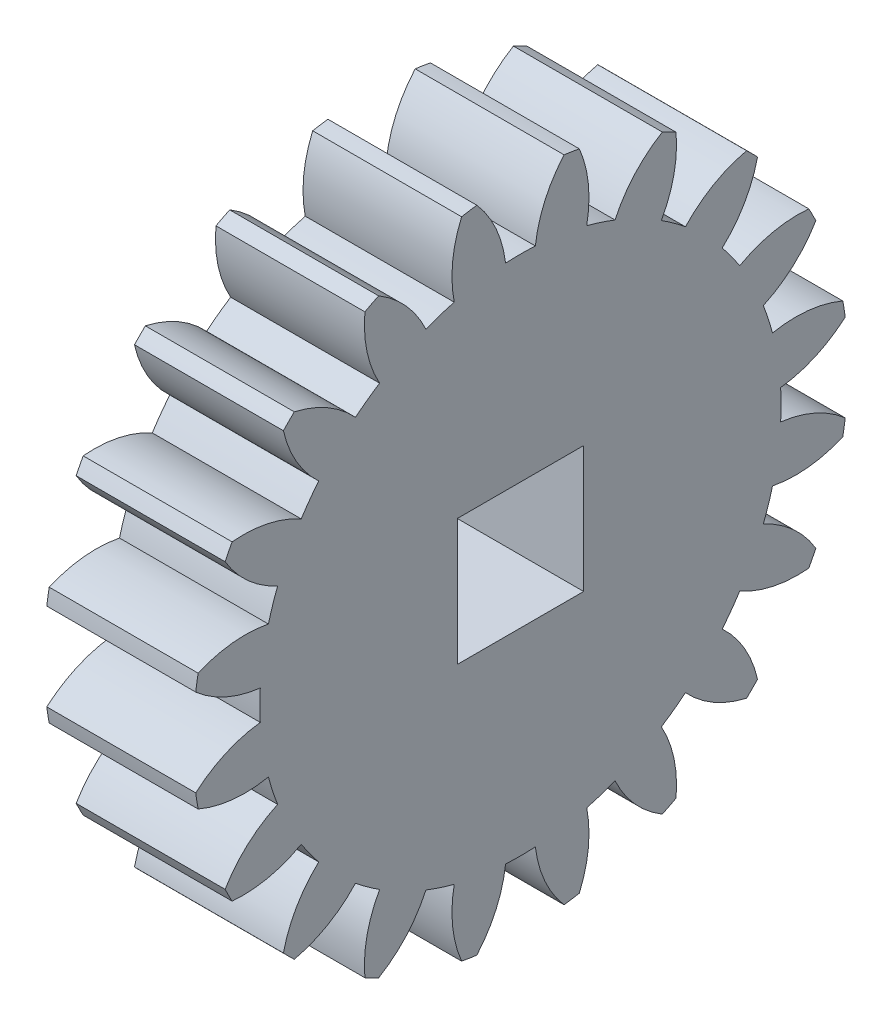
SolidWorks part; units mm, degrees
ref_plane "Plane1" through (0, 0, 0) normal (0, 0, 1) x (1, 0, 0)
ref_plane "Plane2" through (0, 0, 0) normal (0, 1, 0) x (1, 0, 0)
ref_plane "Plane3" through (0, 0, 0) normal (1, 0, 0) x (0, 0, -1)
other "Configuration Table"
sketch "HoldingSke" plane through (0, 0, 0) normal (0, 1, 0) x (1, 0, 0)
  line L0 (0, 0) -> (0.9397, -0.342)
  line L1 (-15, 0) -> (100, 0) construction
  line L2 (0, 0) -> (-2.1039, 2.3779)
  line L3 (0, 0) -> (-11.863, 4.5341)
  line L4 (0, 0) -> (8.1152, 2.9537)
  line L5 (0, 0) -> (-46.8476, -17.4728)
  line L6 (0, 0) -> (-4.1448, -2.7965)
  line L7 (-2.1039, 2.3779) -> (8.6586, 51.2059)
  line L8 (-76.2, 54.61) -> (-76.1, 54.61)
  line L9 (-71.009, 38.7566) -> (-53.1078, 45.2721)
  line L10 (-76.2, 71.12) -> (104.1128, 71.12)
  line L11 (0, 0) -> (-5, 0)
  line L12 (-76.2, 101.6) -> (-76.162, 101.6)
  line L13 (24.9733, 27.94) -> (52.9518, 28.4284)
  line L14 (24.9733, 27.94) -> (24.9743, 27.94)
  line L15 (24.9733, 27.94) -> (100.4006, 29.5858)
  line L16 (-63.627, -1) -> (-12.827, -1)
  circle A0 centre (0, 0) radius 0.4
  circle A1 centre (0, 0) radius 8.749
  circle A2 centre (0, 0) radius 37.5
  circle A3 centre (0, 0) radius 0.4
  dimension "MHD" = 17.498
  dimension "Hub_dia" = 75
  dimension "Bore" = 0.8
  dimension "MBD" = 0.8
  dimension "Num_teeth" = 20
  dimension "Pitch" = 1
  dimension "Overall_len" = 50
  dimension "Show_teeth" = 20
  dimension "Thickness" = 5
  dimension "OAL" = 50.0001
  dimension "T_dim" = 0.1
  dimension "Ap" = 20
  dimension "H" = 19.05
  dimension "Pitch_radius" = 180.3128
  dimension "Width" = 5
  dimension "Backlash" = 0.038
  dimension "Addendum_fac" = 1
  dimension "Dedendum_fac" = 1.25
  dimension "Clearance_fac" = 0.25
  dimension "Dedendum_add" = 0.001
  dimension "Module" = 1
sketch "BasProSke" plane through (0, 0, 0) normal (0, 1, 0) x (1, 0, 0)
  line L0 (-10, 0) -> (60, 0) construction
  line L1 (0, 0) -> (0, 11)
  line L2 (0, 0) -> (5, 0)
  line L3 (5, 0) -> (5, 11)
  line L4 (5, 11) -> (0, 11)
  dimension "Thickness" = 5
  dimension "Diameter" = 22
revolve "Base-Revolve" add sketch "BasProSke" angle 360 about L0
sketch "TooCutSke" plane through (0, 0, 0) normal (1, 0, 0) x (0, 0, -1)
  line L1 (0, 0) -> (0, 107) construction
  line L2 (0, 0) -> (-0.8511, 9.9637) construction
  line L3 (0, 0) -> (-3.1206, 19.7028) construction
  line L4 (-0.8511, 9.9637) -> (-1.5603, 9.8514) construction
  arc A0 (0.4999, 8.7347) -> (-0.4999, 8.7347) centre (0, 0) ccw
  arc A1 (1.4852, 10.9249) -> (-1.4852, 10.9249) centre (0, 0) ccw
  circle A2 centre (0, 0) radius 10 construction
  circle A3 centre (0, 0) radius 9.3969 construction
  arc A4 (-0.4999, 8.7347) -> (-1.4852, 10.9249) centre (-4.4722, 8.2645) ccw
  arc A5 (1.4852, 10.9249) -> (0.4999, 8.7347) centre (4.4722, 8.2645) ccw
  dimension "Root_dia" = 17.498
  dimension "Overcut_dia" = 22.0508
  dimension "Pitch_dia" = 20
  dimension "Base_dia" = 18.7939
  dimension "Flank_rad" = 4
  dimension "Half_ang" = 9
  dimension "Half_CT" = 0.7181
extrude "ToothCut" cut sketch "TooCutSke" along normal through all
fillet "Breaks" [suppressed] radius 0.02
fillet "RootFillets" [suppressed] radius 0.251
pattern_circular "TeethCuts" count 20 every 18 about axis through (-10, 0, 0) along (1, 0, 0) of "ToothCut", "RootFillets", "Breaks"
sketch "HubNeaOneSke" plane through (0, 0, 0) normal (-1, 0, 0) x (0, 0, 1)
  circle A0 centre (0, 0) radius 8.749
  dimension "Diameter" = 17.498
extrude "HubNearOne" [suppressed] add sketch "HubNeaOneSke" along normal blind 45.0001
sketch "HubNeaBotSke" plane through (0, 0, 0) normal (-1, 0, 0) x (0, 0, 1)
  circle A0 centre (0, 0) radius 8.749
  dimension "Diameter" = 17.498
extrude "HubNearBoth" [suppressed] add sketch "HubNeaBotSke" along normal blind 22.5
ref_plane "FarPln" through (5, 0, 0) normal (1, 0, 0) x (0, 0, -1)
sketch "HubFarSke" plane through (5, 0, 0) normal (1, 0, 0) x (0, 0, -1)
  circle A0 centre (0, 0) radius 8.749
  dimension "Diameter" = 17.498
extrude "HubFar" [suppressed] add sketch "HubFarSke" along normal blind 22.5
sketch "BorSke" plane through (0, 0, 0) normal (1, 0, 0) x (0, 0, -1)
  circle A0 centre (0, 0) radius 0.4
  dimension "Diameter" = 0.8
extrude "Bore" cut sketch "BorSke" along normal mid plane 100.0001
sketch "KeySke" plane through (0, 0, 0) normal (1, 0, 0) x (0, 0, -1)
  line L0 (-0.05, 0) -> (-0.05, 0.5)
  line L1 (-0.05, 0.5) -> (0.05, 0.5)
  line L2 (0.05, 0.5) -> (0.05, 0)
  line L3 (0, 0) -> (0, 34) construction
  line L4 (-0.05, 0) -> (0.05, 0)
  dimension "Offset" = 0.5
  dimension "Width" = 0.1
extrude "Keyway" [suppressed] cut sketch "KeySke" along normal mid plane 100.0001
pattern_circular "Keyway2" [suppressed] count 2 every 90 about axis through (-10, 0, 0) along (1, 0, 0)
sketch "Sketch1" plane through (5, 0, 0) normal (1, 0, 0) x (0, 0, -1)
  line L1 (-2.1213, -2.1213) -> (2.1213, -2.1213)
  line L2 (-2.1213, -2.1213) -> (-2.1213, 2.1213)
  line L3 (-2.1213, 2.1213) -> (2.1213, 2.1213)
  line L4 (2.1213, -2.1213) -> (2.1213, 2.1213)
  circle A0 centre (0, 0) radius 3 construction
  dimension "D1" = 6
extrude "Cut-Extrude1" cut sketch "Sketch1" against normal through all
equation "' \"Module@HoldingSke\" = 6.35"
equation "' \"Num_teeth@HoldingSke\" = 12"
equation "' \"Ap@HoldingSke\" =  20"
equation "' \"Ap@HoldingSke\" = 20"
equation "' \"Width@HoldingSke\" = 0.5 * 25.4"
equation "' \"Hub_dia@HoldingSke\"= 1 * 25.4"
equation "' \"Hub_dia@HoldingSke\" = 1 * 25.4"
equation "' \"Overall_len@HoldingSke\" = 1.0 * 25.4"
equation "' \"Bore@HoldingSke\" = 0.75 * 25.4"
equation "' \"T_dim@HoldingSke\" = 0.1 * 25.4"
equation "' \"Width@KeySke\" = 0.25 * 25.4"
equation "' \"Show_teeth@HoldingSke\" = 13"
equation "' \"Backlash@HoldingSke\" = 0.009 * 25.4"
equation "' \"Addendum_fac@HoldingSke\" = 1.0"
equation "' \"Dedendum_fac@HoldingSke\" = 1.25"
equation "' \"Dedendum_add@HoldingSke\" = 0.00005 * 25.4"
equation "' \"Clearance_fac@HoldingSke\" = 0.25"
equation "\"Pitch@HoldingSke\" = 1 / \"Module@HoldingSke\""
equation "\"Overcut_dia@TooCutSke\" = (\"Num_teeth@HoldingSke\" + 2 * \"Addendum_fac@HoldingSke\") / \"Pitch@HoldingSke\" + 0.002 * 25.4"
equation "\"Pitch_dia@TooCutSke\" = \"Num_teeth@HoldingSke\" / \"Pitch@HoldingSke\""
equation "\"Base_dia@TooCutSke\" = \"Num_teeth@HoldingSke\" / \"Pitch@HoldingSke\" * cos((\"Ap@HoldingSke\"  * 3.14159265 / 180))"
equation "\"Root_dia@TooCutSke\" = (\"Num_teeth@HoldingSke\" + 2) / \"Pitch@HoldingSke\" - 2 * (\"Addendum_fac@HoldingSke\" + \"Dedendum_fac@HoldingSke\") / \"Pitch@HoldingSke\" - \"Dedendum_add@HoldingSke\" * 2"
equation "\"Half_ang@TooCutSke\" = 180 / \"Num_teeth@HoldingSke\""
equation "\"Half_CT@TooCutSke\" = \"Num_teeth@HoldingSke\" / \"Pitch@HoldingSke\" * sin((3.14159265 / 2 / \"Num_teeth@HoldingSke\")) / 2 - 7 * \"Backlash@HoldingSke\" / 4"
equation "\"Flank_rad@TooCutSke\" = \"Num_teeth@HoldingSke\" / \"Pitch@HoldingSke\" / 5"
equation "\"Radius@RootFillets\" = \"Clearance_fac@HoldingSke\" / \"Pitch@HoldingSke\" + \"Dedendum_add@HoldingSke\""
equation "\"Break_rad@Breaks\" = 0.02 / \"Pitch@HoldingSke\""
equation "\"Thickness@HoldingSke\" = \"Width@HoldingSke\""
equation "\"OAL@HoldingSke\" = \"Thickness@HoldingSke\""
equation "\"MHD@HoldingSke\" = (\"Num_teeth@HoldingSke\" + 2) / \"Pitch@HoldingSke\" - 2 * (\"Addendum_fac@HoldingSke\" + \"Dedendum_fac@HoldingSke\")  / \"Pitch@HoldingSke\" - \"Dedendum_add@HoldingSke\" * 2"
equation "\"MBD@HoldingSke\" = (\"Num_teeth@HoldingSke\" + 2) / \"Pitch@HoldingSke\" - 2 * (\"Addendum_fac@HoldingSke\" + \"Dedendum_fac@HoldingSke\")  / \"Pitch@HoldingSke\" - \"Dedendum_add@HoldingSke\" * 2 - 0.002 * 25.4"
equation "\"MHD@HoldingSke\" = ((sgn( \"MHD@HoldingSke\" - \"Hub_dia@HoldingSke\" )-1)*( \"MHD@HoldingSke\" - \"Hub_dia@HoldingSke\" ))/-2+ \"Hub_dia@HoldingSke\""
equation "\"MBD@HoldingSke\" = ((sgn( \"MBD@HoldingSke\" - \"Bore@HoldingSke\" )-1)*( \"MBD@HoldingSke\" - \"Bore@HoldingSke\" ))/-2+ \"Bore@HoldingSke\""
equation "\"OAL@HoldingSke\" = ((sgn( \"OAL@HoldingSke\" - \"Overall_len@HoldingSke\" )+1)*( \"OAL@HoldingSke\" - \"Overall_len@HoldingSke\" ))/2 + \"Overall_len@HoldingSke\" + 0.000002 * 25.4"
equation "\"Num_teeth@TeethCuts\" = int( \"Show_teeth@HoldingSke\" ) + 1"
equation "\"Num_teeth@TeethCuts\" = ((sgn( \"Num_teeth@TeethCuts\" - \"Num_teeth@HoldingSke\" )-1)*( \"Num_teeth@TeethCuts\" - \"Num_teeth@HoldingSke\" ))/-2+ \"Num_teeth@HoldingSke\""
equation "\"Num_teeth@TeethCuts\" = ((sgn( \"Num_teeth@TeethCuts\" - 2.0)+1)*( \"Num_teeth@TeethCuts\" - 2.0))/2 +2.0"
equation "\"Angle@TeethCuts\" = 360.0 / \"Num_teeth@HoldingSke\""
equation "\"Diameter@BasProSke\" = (\"Num_teeth@HoldingSke\" + 2 * \"Addendum_fac@HoldingSke\") / \"Pitch@HoldingSke\""
equation "\"Thickness@BasProSke\"  = \"Thickness@HoldingSke\""
equation "' \"Fillet_rad@BasProSke\" =  \"Thickness@HoldingSke\" * 0.05"
equation "' \"Fillet_rad@BasProSke\" = \"Thickness@HoldingSke\" * 0.05"
equation "\"MHD@HoldingSke\" = ((sgn( \"MHD@HoldingSke\" - \"Root_dia@TooCutSke\" )-1)*( \"MHD@HoldingSke\" - \"Root_dia@TooCutSke\" ))/-2+ \"Root_dia@TooCutSke\""
equation "\"Diameter@HubNeaOneSke\" = \"MHD@HoldingSke\""
equation "\"Length@HubNearOne\" = \"OAL@HoldingSke\" - \"Thickness@BasProSke\""
equation "\"Diameter@HubNeaBotSke\" = \"MHD@HoldingSke\""
equation "\"Length@HubNearBoth\" = ( \"OAL@HoldingSke\" - \"Thickness@BasProSke\" ) / 2.0"
equation "\"Thickness@FarPln\" = \"Thickness@BasProSke\""
equation "\"Diameter@HubFarSke\" = \"MHD@HoldingSke\""
equation "\"Length@HubFar\" = ( \"OAL@HoldingSke\" - \"Thickness@BasProSke\" ) / 2.0"
equation "\"Diameter@BorSke\" = \"MBD@HoldingSke\""
equation "\"D1@Bore\" = \"OAL@HoldingSke\" * 2.0"
equation "\"D1@Keyway\" = \"OAL@HoldingSke\" * 2.0"
equation "\"Offset@KeySke\" = \"T_dim@HoldingSke\" + \"MBD@HoldingSke\" / 2.0"
